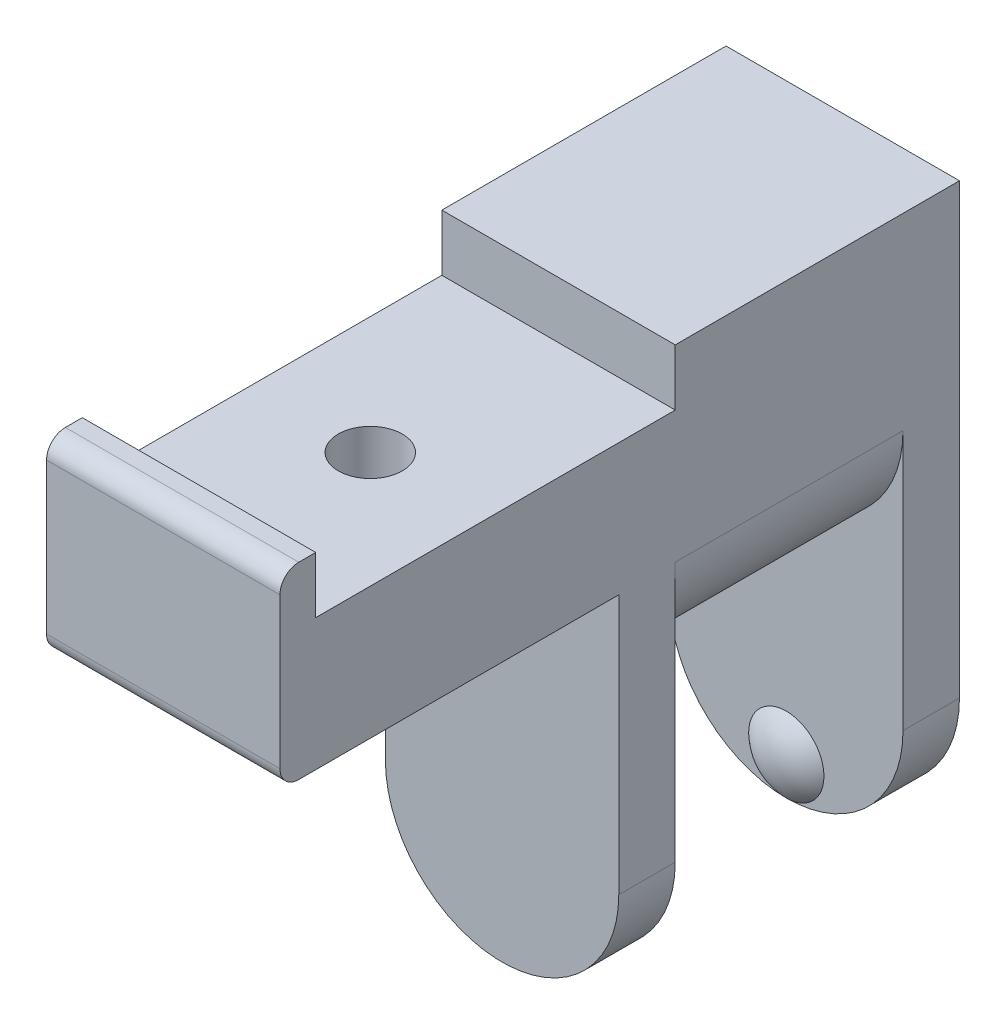
SolidWorks part; units mm, degrees
ref_plane "Спереди" through (0, 0, 0) normal (0, 0, 1) x (1, 0, 0)
ref_plane "Сверху" through (0, 0, 0) normal (0, 1, 0) x (1, 0, 0)
ref_plane "Справа" through (0, 0, 0) normal (1, 0, 0) x (0, 0, -1)
sketch "Эскиз2" plane through (0, 0, 0) normal (1, 0, 0) x (0, 0, -1)
  line L0 (12.1, -20) -> (15.1, -20)
  line L1 (15.1, -20) -> (15.1, 10)
  line L2 (15.1, 10) -> (0, 10)
  line L3 (-21, 10) -> (-21, 0)
  line L4 (-21, 0) -> (-3, 0)
  line L5 (-3, 0) -> (-3, -20)
  line L6 (-3, -20) -> (0, -20)
  line L7 (0, -20) -> (0, 0)
  line L8 (0, 0) -> (12.1, 0)
  line L9 (12.1, 0) -> (12.1, -20)
  line L10 (0, -8) -> (12.1, -8)
  line L11 (-19.1, 10) -> (-19.1, 7)
  line L12 (-19.1, 7) -> (0, 7)
  line L13 (0, 7) -> (0, 10)
  line L14 (-19.1, 10) -> (-21, 10)
  dimension "D1" = 30
  dimension "D2" = 20
  dimension "D3" = 3
  dimension "D4" = 12.1
  dimension "D5" = 8
  dimension "D6" = 10
  dimension "D7" = 19.1
  dimension "D8" = 1.9
  dimension "D9" = 3
extrude "Бобышка-Вытянуть1" add sketch "Эскиз2" along normal blind 12.4 contours L11 L14 L3 L4 L5 L6 L7 L8 L9 L0 L1 L2 L13 L12 | L7 L10 L9 L8
sketch "Эскиз3" plane through (0, 0, 0) normal (0, 0, 1) x (1, 0, 0)
  line L0 (0, 0) -> (12.4, 0) construction
  line L1 (0, 0) -> (-4.3102, 0)
  line L2 (-4.3102, 0) -> (-4.3102, -10.1582)
  line L3 (-4.3102, -10.1582) -> (16.7843, -10.1582)
  line L4 (16.7843, -10.1582) -> (16.7843, 0)
  line L5 (16.7843, 0) -> (12.4, 0)
  arc A0 (0, 0) -> (12.4, 0) centre (6.2, 0) ccw
  dimension "D1" = 6.2
  dimension "D2" = 16.7843
  dimension "D3" = 4.3102
  dimension "D4" = 10.1582
extrude "Вырез-Вытянуть1" cut sketch "Эскиз3" against normal up to surface (12.1 mm away) up to face at (6.2, -14, -12.1)
sketch "Эскиз4" plane through (0, 0, 0) normal (0, 0, 1) x (1, 0, 0)
  line L0 (0, -13.8) -> (12.4, -13.8) construction
  line L1 (0, 0) -> (0, -20) construction
  line L2 (12.4, -20) -> (12.4, 0) construction
  line L3 (12.4, -20) -> (0, -20) construction
  line L4 (0, -13.8) -> (-4.5292, -13.8)
  line L5 (-4.5292, -13.8) -> (-4.5292, -23.0327)
  line L6 (-4.5292, -23.0327) -> (17.4573, -23.0327)
  line L7 (17.4573, -23.0327) -> (17.4573, -13.8)
  line L8 (17.4573, -13.8) -> (12.4, -13.8)
  arc A0 (0, -13.8) -> (12.4, -13.8) centre (6.2, -13.8) ccw
  dimension "D1" = 17.4573
  dimension "D2" = 4.5292
  dimension "D3" = 23.0327
extrude "Вырез-Вытянуть2" cut sketch "Эскиз4" against normal through all both and the other way through all
hole_wizard "Отверстие с зазором M31" positions "Эскиз7" profile "Эскиз8" hole size "M3" standard "IS"
sketch "Эскиз7" plane through (0, 7, 0) normal (0, 1, 0) x (1, 0, 0)
  line L0 (12.4, 0) -> (0, 0) construction
  line L1 (0, -19.1) -> (0, 0) construction
  point P0 (6.25, -10.05)
  dimension "D1" = 10.05
  dimension "D2" = 6.25
sketch "Эскиз8" plane through (6.25, 7, 10.05) normal (1, 0, 0) x (0, 0, 1)
  line L0 (0, 0) -> (0, 11.0215)
  line L1 (0, 11.0215) -> (1.7, 10)
  line L2 (1.7, 10) -> (1.7, 0)
  line L5 (1.7, 0) -> (0, 0)
  line L10 (0, 11.0215) -> (-1.7, 10) construction
  line L11 (0, -6.35) -> (0, 107.95) construction
  dimension "Диаметр отверстия" = 3.4
  dimension "Глубина отверстия" = 10
  dimension "Угол заточки сверла" = 118
fillet "Скругление1" radius 1 2 edges at (6.2, 0, 21) (6.2, 10, 21)
ref_plane "Плоскость1" through (6.2, 0, 0) normal (1, 0, 0) x (0, 0, -1)
sketch "Эскиз9" plane through (6.2, 0, 0) normal (1, 0, 0) x (0, 0, -1)
  line L0 (12.1, -20) -> (12.1, -18)
  line L1 (11.3, -18) -> (12.1, -18)
  line L2 (12.1, 0) -> (12.1, -13.8) construction
  arc A0 (12.1, -20) -> (11.3, -18) centre (14.2, -18) cw
  point P4 (6.4984, -11.1713)
  dimension "D1" = 0.8
  dimension "D2" = 2
revolve "Повернуть1" add sketch "Эскиз9" angle 360 about L1
